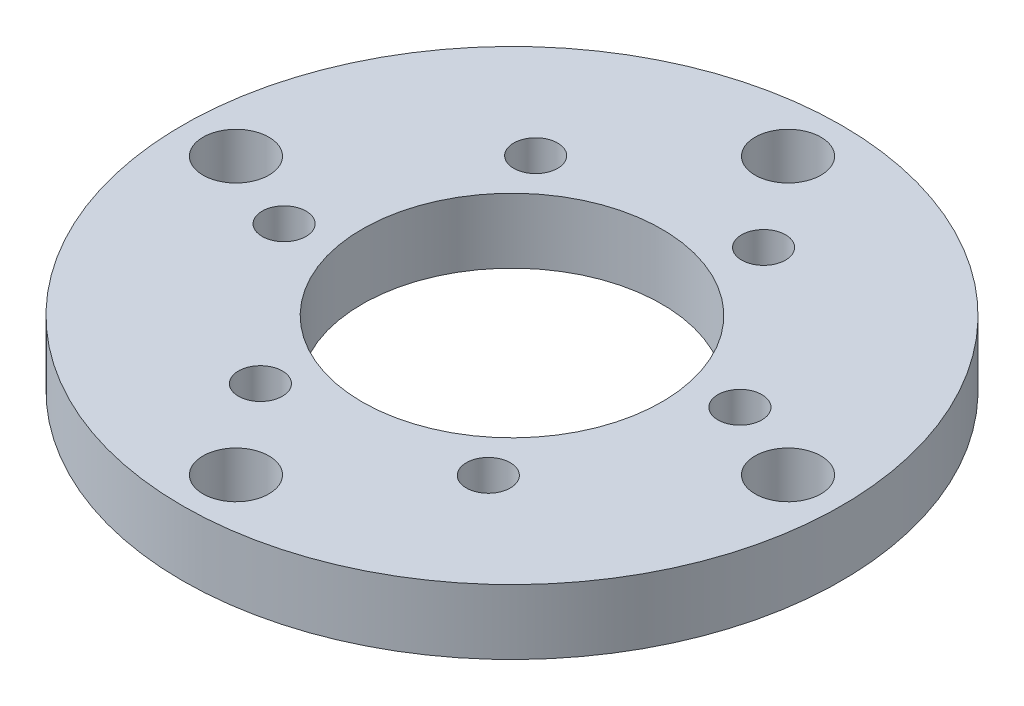
SolidWorks part; units mm, degrees
ref_plane "Front Plane" through (0, 0, 0) normal (0, 0, 1) x (1, 0, 0)
ref_plane "Top Plane" through (0, 0, 0) normal (0, 1, 0) x (1, 0, 0)
ref_plane "Right Plane" through (0, 0, 0) normal (1, 0, 0) x (0, 0, -1)
sketch "Sketch1" plane through (0, 0, 0) normal (0, 1, 0) x (1, 0, 0)
  line L1 (0, 0) -> (88.9, 0)
  line L2 (0, 0) -> (0, -88.9)
  line L3 (0, -88.9) -> (88.9, -88.9)
  line L4 (88.9, 0) -> (88.9, -88.9)
  dimension "D1" = 88.9
  dimension "D2" = 88.9
extrude "Boss-Extrude1" add sketch "Sketch1" against normal blind 8.255
ref_point "Point1"
sketch "Sketch5" plane through (0, 0, 0) normal (0, 1, 0) x (1, 0, 0)
  line L0 (0, 0) -> (0, -88.9)
  line L1 (0, -88.9) -> (88.9, -88.9)
  line L2 (88.9, -88.9) -> (88.9, 0)
  line L3 (88.9, 0) -> (0, 0)
  circle A0 centre (44.45, -44.45) radius 41.91
  dimension "D1" = 83.82
extrude "Cut-Extrude5" cut sketch "Sketch5" against normal blind 8.255
sketch "Sketch8" plane through (0, 0, 0) normal (0, 1, 0) x (1, 0, 0)
  circle A0 centre (44.45, -44.45) radius 19.05
  dimension "D1" = 38.1
ref_point "Point2"
sketch "Sketch9" plane through (0, 0, 0) normal (0, 1, 0) x (1, 0, 0)
  circle A1 centre (44.45, -79.5528) radius 4.191
extrude "Cut-Extrude7" cut sketch "Sketch9" against normal blind 8.255
pattern_circular "CirPattern1" count 4 over 360 about axis through (44.45, 0, 44.45) along (0, 1, 0) of "Cut-Extrude7"
sketch "Sketch11" plane through (0, 0, 0) normal (0, 1, 0) x (1, 0, 0)
  line L0 (44.45, -44.45) -> (30.1921, -83.8601)
  circle A0 centre (44.45, -44.45) radius 41.91 construction
  circle A1 centre (35.9499, -67.945) radius 2.794
  dimension "D1" = 5.588
  dimension "D2" = 23.495
extrude "Cut-Extrude9" cut sketch "Sketch11" against normal blind 8.255 contours L0 A1 | L0 A1
pattern_circular "CirPattern3" count 6 over 360 about axis through (44.45, 0, 44.45) along (0, 1, 0) of "Cut-Extrude9"
extrude "Cut-Extrude10" cut sketch "Sketch8" against normal blind 8.255
sketch "Sketch13" plane through (0, 0, 0) normal (0, 1, 0) x (1, 0, 0)
  line L1 (-6.35, 6.35) -> (95.25, 6.35)
  line L2 (-6.35, 6.35) -> (-6.35, -95.25)
  line L3 (-6.35, -95.25) -> (95.25, -95.25)
  line L4 (95.25, 6.35) -> (95.25, -95.25)
  line L5 (-6.35, 6.35) -> (95.25, -95.25) construction
  line L6 (-6.35, -95.25) -> (95.25, 6.35) construction
  line L7 (12.7, -12.7) -> (76.2, -12.7)
  line L8 (12.7, -12.7) -> (12.7, -76.2)
  line L9 (12.7, -76.2) -> (76.2, -76.2)
  line L10 (76.2, -12.7) -> (76.2, -76.2)
  line L11 (12.7, -12.7) -> (76.2, -76.2) construction
  line L12 (12.7, -76.2) -> (76.2, -12.7) construction
  point P0 (44.45, -44.45)
  point P5 (44.45, -44.45)
  dimension "D1" = 101.6
  dimension "D2" = 101.6
  dimension "D3" = 63.5
